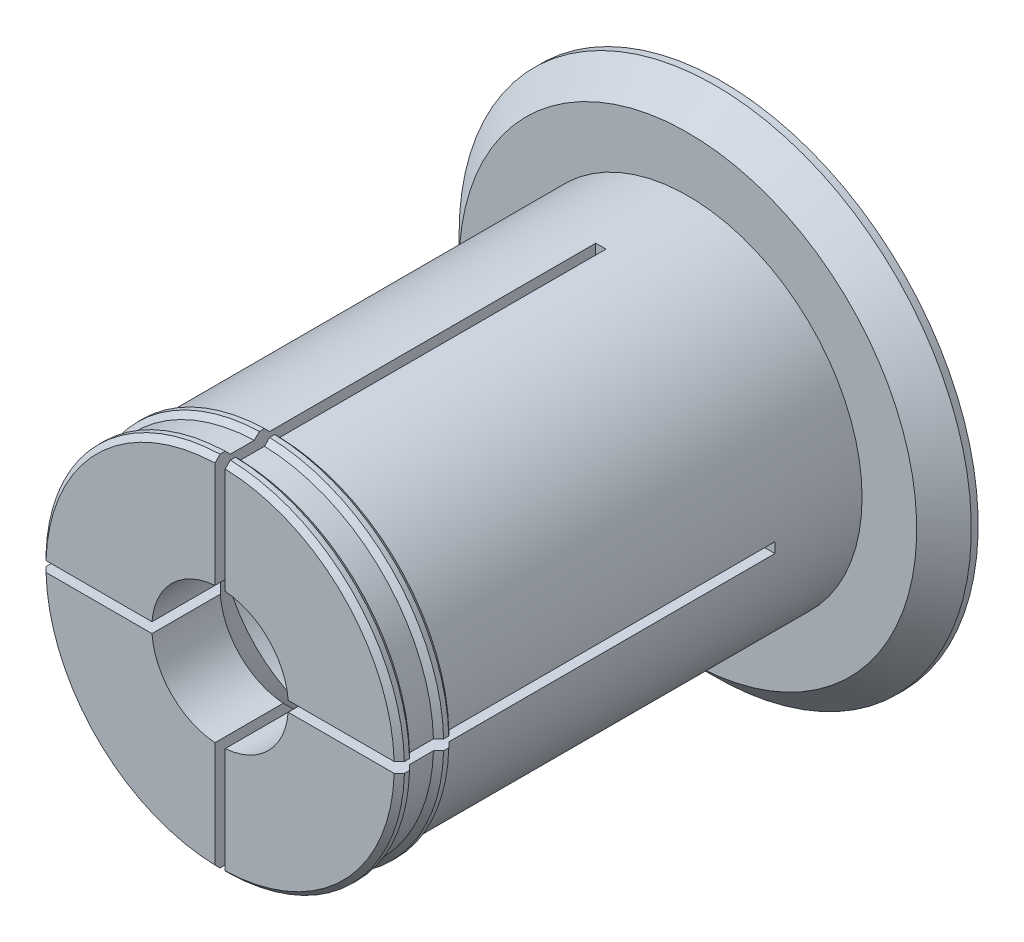
SolidWorks part; units mm, degrees
ref_plane "Front" through (0, 0, 0) normal (0, 0, 1) x (1, 0, 0)
ref_plane "Top" through (0, 0, 0) normal (0, 1, 0) x (1, 0, 0)
ref_plane "Right" through (0, 0, 0) normal (1, 0, 0) x (0, 0, -1)
sketch "Axle base sketch" plane through (0, 0, 0) normal (0, 0, 1) x (1, 0, 0)
  circle A0 centre (0, 0) radius 25.5
  dimension "D1" = 51
extrude "Axle" add sketch "Axle base sketch" along normal blind 68.5
sketch "Guard base" plane through (0, 0, 0) normal (0, 0, -1) x (-1, 0, 0)
  circle A0 centre (0, 0) radius 37.5
  dimension "D1" = 75
extrude "Guard" add sketch "Guard base" along normal blind 5
sketch "Inner axle hole base" plane through (0, 0, 68.5) normal (0, 0, 1) x (1, 0, 0)
  circle A0 centre (0, 0) radius 10
  dimension "D1" = 20
extrude "Inner axle hole" cut sketch "Inner axle hole base" against normal through all
sketch "Mate ring base" plane through (0, 0, 0) normal (0, 1, 0) x (1, 0, 0)
  line L0 (25.5, -68.5) -> (26.25, -67.75)
  line L1 (26.25, -67.75) -> (26.25, -67)
  line L2 (26.25, -67) -> (25.5, -66.25)
  line L3 (26.25, -67.75) -> (26.25, -68.5) construction
  line L4 (26.25, -68.5) -> (25.5, -68.5) construction
  line L5 (25.5, -66.25) -> (25.5, -68.5)
  line L6 (25.5, -68.5) -> (25.5, 0) construction
  line L8 (25.5, -62.75) -> (26.25, -62)
  line L9 (26.25, -62) -> (26.25, -61.25)
  line L10 (26.25, -61.25) -> (25.5, -60.5)
  line L11 (25.5, -60.5) -> (25.5, -62.75)
  dimension "D1" = 0.75
  dimension "D2" = 0.75
  dimension "D3" = 5
  dimension "D4" = 0.75
ref_axis "Center Z" through (0, 0, 0) along (0, 0, -1)
revolve "Mate rings" add sketch "Mate ring base" angle 360 about axis through (0, 0, 0) along (0, 0, -1)
sketch "Inner mass remove base" plane through (0, 0, 0) normal (1, 0, 0) x (0, 0, -1)
  line L0 (-68.5, 0) -> (-50.75, -17.75)
  line L1 (-50.75, -17.75) -> (-12.75, -17.75)
  line L2 (-12.75, -17.75) -> (5, 0)
  line L3 (5, 0) -> (-68.5, 0)
  line L4 (5, -10) -> (5, 10) construction
  line L5 (-50.75, -17.75) -> (-50.75, -10) construction
  line L6 (-50.75, -17.75) -> (-50.75, -25.5) construction
  line L7 (-68.5, 10) -> (-68.5, -10) construction
  point P9 (-68.5, -10)
  point P11 (-68.5, -25.5)
  dimension "D1" = 135
revolve "Inner mass remove" cut sketch "Inner mass remove base" angle 360 about axis through (0, 0, 0) along (0, 0, -1)
ref_point "Bend room endpoint"
sketch "Bend room base" plane through (0, 0, 68.5) normal (0, 0, 1) x (1, 0, 0)
  line L0 (0.75, -37.5) -> (0.75, 37.5)
  line L1 (0.75, 37.5) -> (-0.75, 37.5)
  line L2 (-0.75, 37.5) -> (-0.75, -37.5)
  line L3 (-0.75, -37.5) -> (0.75, -37.5)
  dimension "D1" = 0.75
  dimension "D2" = 0.75
  dimension "D3" = 37.5
  dimension "D4" = 37.5
extrude "Bend room 1" cut sketch "Bend room base" against normal up to vertex (28.9925 mm away)
pattern_circular "Bend room 2" count 2 every 90 about axis through (0, 0, 0) along (0, 0, -1) of "Bend room 1"
chamfer "Easy removal chamfer" distance 4 angle 45 1 edges at (-37.5, 0, 0)
equation "\"32_92_spool_inner_diameter\"=32"
equation "\"D1@Axle base sketch\"=\"52_62_spool_inner_diameter\"- \"spool_inner_diameter_room\""
equation "\"spool_inner_diameter_room\"=1"
equation "\"32_92_spool_thickness\"=92"
equation "\"D1@Axle\"=\"52_62_spool_thickness\"+\"guard_thickness\"+\"removal_room\"*2"
equation "\"32_92_guard_diameter\"=50"
equation "\"D1@Guard base\"=\"52_62_guard_diameter\""
equation "\"guard_thickness\"=5"
equation "\"D1@Guard\"=\"guard_thickness\""
equation "\"large_inner_axle_diameter\"=20"
equation "\"D1@Inner axle hole base\"=\"large_inner_axle_diameter\""
equation "\"mate_room\"= 0.25"
equation "\"removal_room\"= 0.75"
equation "\"small_inner_axle_diameter\"=17"
equation "\"53_55_spool_inner_diameter\"=53"
equation "\"53_55_spool_thickness\"=55"
equation "\"53_55_guard_diameter\"=75"
equation "\"D1@Mate ring base\"=\"removal_room\""
equation "\"D2@Mate ring base\"=\"removal_room\""
equation "\"D3@Mate ring base\"=\"guard_thickness\""
equation "\"D4@Mate ring base\"=\"removal_room\""
equation "\"D1@Bend room base\" = \"removal_room\""
equation "\"D2@Bend room base\"=\"removal_room\""
equation "\"D3@Bend room base\"=\"52_62_guard_diameter\"/2"
equation "\"D4@Bend room base\"=\"52_62_guard_diameter\"/2"
equation "\"bend_room_length_multiplier\"=3"
equation "\"D1@Easy removal chamfer\"=\"guard_thickness\"-1"
equation "\"32_92_extra_spool_thickness\"=-5"
equation "\"39_92_spool_inner_diameter\"=39"
equation "\"39_92_spool_thickness\"=92"
equation "\"39_92_guard_diameter\"=60"
equation "\"52_62_spool_inner_diameter\"=52"
equation "\"52_62_spool_thickness\"=62"
equation "\"52_62_guard_diameter\"=75"
